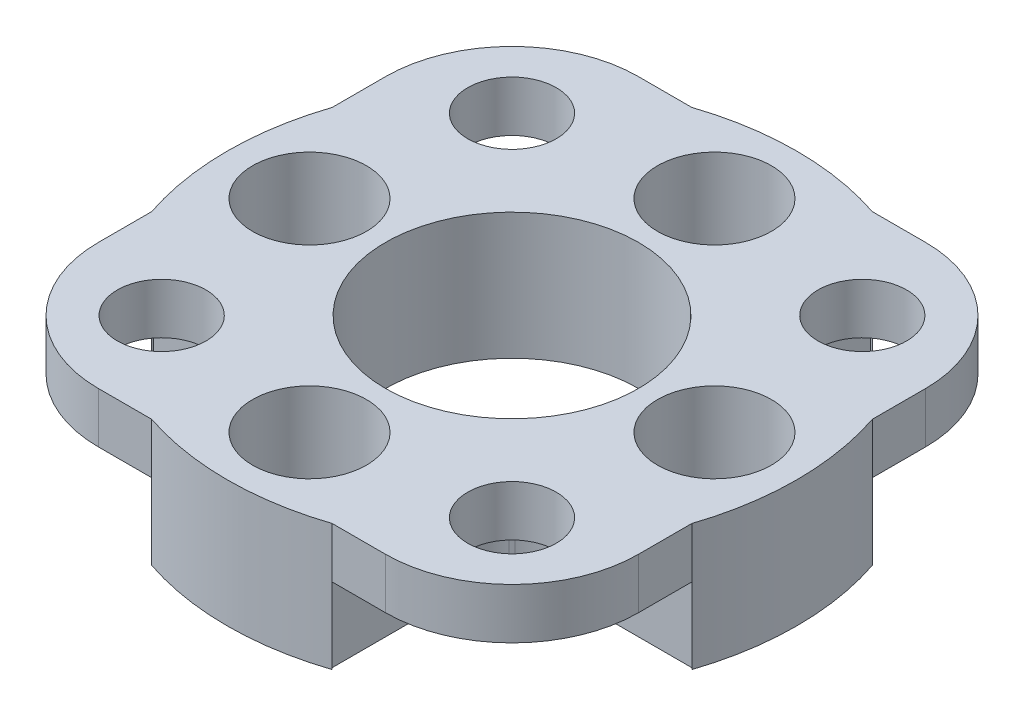
SolidWorks part; units mm, degrees
ref_plane "Plan de face" through (0, 0, 0) normal (0, 0, 1) x (1, 0, 0)
ref_plane "Plan de dessus" through (0, 0, 0) normal (0, 1, 0) x (1, 0, 0)
ref_plane "Plan de droite" through (0, 0, 0) normal (1, 0, 0) x (0, 0, -1)
sketch "Esquisse1" plane through (0, 0, 0) normal (0, 1, 0) x (1, 0, 0)
  circle A0 centre (0, 0) radius 11.25
  dimension "D1" = 22.5
extrude "Boss.-Extru.1" add sketch "Esquisse1" along normal blind 2
sketch "Esquisse8" plane through (0, 0, 0) normal (0, -1, 0) x (1, 0, 0)
  circle A0 centre (0, 0) radius 11.25
  circle A1 centre (0, 0) radius 11.25 construction
extrude "Boss.-Extru.2" add sketch "Esquisse8" along normal blind 3
sketch "Esquisse15" plane through (0, 2, 0) normal (0, 1, 0) x (1, 0, 0)
  line L1 (-10.67, 10.67) -> (10.67, 10.67)
  line L2 (-10.67, 10.67) -> (-10.67, -10.67)
  line L3 (-10.67, -10.67) -> (10.67, -10.67)
  line L4 (10.67, 10.67) -> (10.67, -10.67)
  point P4 (0, 10.67)
  point P6 (10.67, 0)
  dimension "D1" = 21.34
extrude "Boss.-Extru.3" add sketch "Esquisse15" against normal blind 2
sketch "Esquisse14" plane through (0, -3, 0) normal (0, -1, 0) x (1, 0, 0)
  circle A0 centre (0, 0) radius 5
  dimension "D1" = 10
extrude "Enlèv. mat.-Extru.3" cut sketch "Esquisse14" against normal blind 6
hole_wizard "Dégagement M21" positions "Esquisse16" profile "Esquisse17" size "M2" standard "Ansi Metric" slot yes end condition through all
sketch "Esquisse16" plane through (0, 2, 0) normal (0, 1, 0) x (1, 0, 0)
  line L0 (10.67, -10.67) -> (10.67, -3.5656) construction
  line L1 (3.5656, -10.67) -> (10.67, -10.67) construction
  line L2 (-3.5656, 10.67) -> (-10.67, 10.67) construction
  line L3 (-10.67, 10.67) -> (-10.67, 3.5656) construction
  point P0 (6.92, -6.92)
  point P2 (-6.92, -6.92)
  point P4 (-6.92, 6.92)
  point P6 (6.92, 6.92)
  dimension "D1" = 3.75
  dimension "D2" = 3.75
  dimension "D3" = 3.75
  dimension "D4" = 3.75
sketch "Esquisse17" plane through (6.92, 2, 6.92) normal (1, 0, 0) x (0, 0, 1)
  line L0 (0, 0) -> (0, 5)
  line L1 (0, 5) -> (1.75, 5)
  line L2 (1.75, 5) -> (1.75, 0)
  line L5 (1.75, 0) -> (0, 0)
  line L11 (0, -6.35) -> (0, 107.95) construction
  dimension "Diamètre du perçage jusqu'au prochain" = 3.5
  dimension "Profondeur du perçage jusqu'au prochain" = 5
sketch "Esquisse18" plane through (0, 0, 0) normal (0, -1, 0) x (1, 0, 0)
  line L0 (-3.5, -10.67) -> (-3.5, -5)
  line L1 (-10.67, 10.67) -> (-3.5, 10.67)
  line L2 (-10.67, 10.67) -> (-10.67, 3.5)
  line L3 (-10.67, 3.5) -> (-5, 3.5)
  line L4 (-3.5, 10.67) -> (-3.5, 5)
  line L5 (10.67, 10.67) -> (3.5, 10.67)
  line L6 (10.67, 10.67) -> (10.67, 3.5)
  line L7 (10.67, 3.5) -> (5, 3.5)
  line L8 (3.5, 10.67) -> (3.5, 5)
  line L9 (10.67, -10.67) -> (3.5, -10.67)
  line L10 (10.67, -10.67) -> (10.67, -3.5)
  line L11 (10.67, -3.5) -> (5, -3.5)
  line L12 (3.5, -10.67) -> (3.5, -5)
  line L13 (-10.67, -10.67) -> (-3.5, -10.67)
  line L14 (-10.67, -10.67) -> (-10.67, -3.5)
  line L15 (-10.67, -3.5) -> (-5, -3.5)
  line L17 (-3.5, 5) -> (3.5, 5)
  line L19 (-3.5, -5) -> (3.5, -5)
  line L22 (5, 3.5) -> (5, -3.5)
  line L24 (-5, 3.5) -> (-5, -3.5)
  circle A2 centre (0, 0) radius 5 construction
  point P18 (5, 0)
  point P30 (-5, 0)
  point P31 (0, 5)
  point P32 (0, -5)
  dimension "D1" = 7
  dimension "D2" = 7
extrude "Enlèv. mat.-Extru.11" cut sketch "Esquisse18" along normal blind 3
fillet "Congé1" radius 5 4 edges at (-10.67, 1, -10.67) (10.67, 1, -10.67) (10.67, 1, 10.67) (-10.67, 1, 10.67)
sketch "Esquisse20" plane through (0, 0, 0) normal (0, -1, 0) x (1, 0, 0)
  circle A0 centre (0, 0) radius 5
  circle A1 centre (0, 0) radius 6.1033
  arc A2 (5, 0) -> (0, 5) centre (0, 0) ccw construction
extrude "Boss.-Extru.5" add sketch "Esquisse20" along normal blind 3
fillet "Congé3" radius 2.5 8 edges at (-5, -1.5, -3.5) (-3.5, -1.5, -5) (3.5, -1.5, -5) (5, -1.5, -3.5) (5, -1.5, 3.5) (3.5, -1.5, 5) (-3.5, -1.5, 5) (-5, -1.5, 3.5)
hole_wizard "Chambrage pour vis à tête cylindrique à 6 pans creux (ou vis CHC) M21" positions "Esquisse12" profile "Esquisse13" counterbore size "M2" standard "Ansi Metric" end condition through all
sketch "Esquisse12" plane through (0, 2, 0) normal (0, 1, 0) x (1, 0, 0)
  line L0 (-8, 0) -> (0, 0) construction
  line L1 (0, 0) -> (0, -8) construction
  line L3 (0, 0) -> (8, 0) construction
  point P0 (-8, 0)
  point P2 (0, -8)
  point P4 (8, 0)
  point P19 (0, 8)
  dimension "D1" = 8
  dimension "D2" = 8
sketch "Esquisse13" plane through (-8, 2, 0) normal (1, 0, 0) x (0, 0, 1)
  line L0 (0, 0) -> (0, 5)
  line L1 (0, 5) -> (1.25, 5)
  line L3 (1.25, 5) -> (1.25, 3.3)
  line L4 (1.25, 3.3) -> (2.25, 3.3)
  line L5 (2.25, 3.3) -> (2.25, 0)
  line L7 (2.25, 0) -> (0, 0)
  line L11 (0, -6.35) -> (0, 107.95) construction
  dimension "Diamètre du perçage jusqu'au prochain" = 2.5
  dimension "Profondeur du perçage jusqu'au prochain" = 5
  dimension "Diamètre du chambrage" = 4.5
  dimension "Profondeur du chambrage" = 3.3
